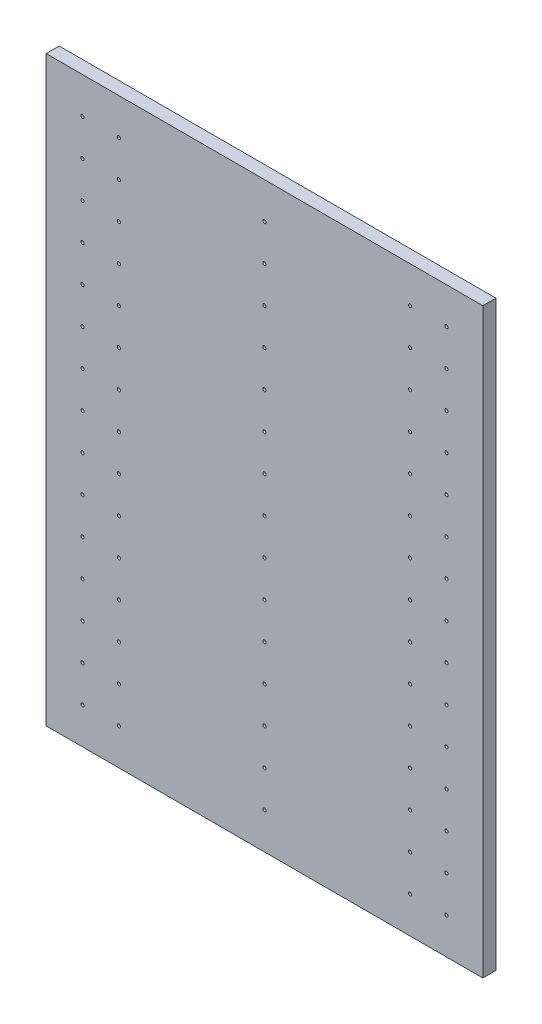
SolidWorks part; units mm, degrees
ref_plane "Спереди" through (0, 0, 0) normal (0, 0, 1) x (1, 0, 0)
ref_plane "Сверху" through (0, 0, 0) normal (0, 1, 0) x (1, 0, 0)
ref_plane "Справа" through (0, 0, 0) normal (1, 0, 0) x (0, 0, -1)
sketch "Эскиз1" plane through (0, 0, 0) normal (0, 0, 1) x (1, 0, 0)
  line L1 (0, 0) -> (600, 0)
  line L2 (0, 0) -> (0, 800)
  line L3 (0, 800) -> (600, 800)
  line L4 (600, 0) -> (600, 800)
extrude "Бобышка-Вытянуть1" add sketch "Эскиз1" along normal blind 18
sketch "Эскиз2" plane through (0, 0, 18) normal (0, 0, 1) x (1, 0, 0)
  circle A0 centre (550, 50) radius 2.25
  circle A1 centre (500, 50) radius 2.25
  circle A2 centre (300, 50) radius 2.25
  circle A3 centre (100, 50) radius 2.25
  circle A4 centre (50, 50) radius 2.25
  circle A60 centre (550, 100) radius 2.25
  circle A61 centre (500, 100) radius 2.25
  circle A62 centre (300, 100) radius 2.25
  circle A63 centre (100, 100) radius 2.25
  circle A64 centre (50, 100) radius 2.25
  circle A65 centre (550, 150) radius 2.25
  circle A66 centre (500, 150) radius 2.25
  circle A67 centre (300, 150) radius 2.25
  circle A68 centre (100, 150) radius 2.25
  circle A69 centre (50, 150) radius 2.25
  circle A70 centre (550, 200) radius 2.25
  circle A71 centre (500, 200) radius 2.25
  circle A72 centre (300, 200) radius 2.25
  circle A73 centre (100, 200) radius 2.25
  circle A74 centre (50, 200) radius 2.25
  circle A75 centre (550, 250) radius 2.25
  circle A76 centre (500, 250) radius 2.25
  circle A77 centre (300, 250) radius 2.25
  circle A78 centre (100, 250) radius 2.25
  circle A79 centre (50, 250) radius 2.25
  circle A80 centre (550, 300) radius 2.25
  circle A81 centre (500, 300) radius 2.25
  circle A82 centre (300, 300) radius 2.25
  circle A83 centre (100, 300) radius 2.25
  circle A84 centre (50, 300) radius 2.25
  circle A85 centre (550, 350) radius 2.25
  circle A86 centre (500, 350) radius 2.25
  circle A87 centre (300, 350) radius 2.25
  circle A88 centre (100, 350) radius 2.25
  circle A89 centre (50, 350) radius 2.25
  circle A90 centre (550, 400) radius 2.25
  circle A91 centre (500, 400) radius 2.25
  circle A92 centre (300, 400) radius 2.25
  circle A93 centre (100, 400) radius 2.25
  circle A94 centre (50, 400) radius 2.25
  circle A95 centre (550, 450) radius 2.25
  circle A96 centre (500, 450) radius 2.25
  circle A97 centre (300, 450) radius 2.25
  circle A98 centre (100, 450) radius 2.25
  circle A99 centre (50, 450) radius 2.25
  circle A100 centre (550, 500) radius 2.25
  circle A101 centre (500, 500) radius 2.25
  circle A102 centre (300, 500) radius 2.25
  circle A103 centre (100, 500) radius 2.25
  circle A104 centre (50, 500) radius 2.25
  circle A105 centre (550, 550) radius 2.25
  circle A106 centre (500, 550) radius 2.25
  circle A107 centre (300, 550) radius 2.25
  circle A108 centre (100, 550) radius 2.25
  circle A109 centre (50, 550) radius 2.25
  circle A110 centre (550, 600) radius 2.25
  circle A111 centre (500, 600) radius 2.25
  circle A112 centre (300, 600) radius 2.25
  circle A113 centre (100, 600) radius 2.25
  circle A114 centre (50, 600) radius 2.25
  circle A115 centre (550, 650) radius 2.25
  circle A116 centre (500, 650) radius 2.25
  circle A117 centre (300, 650) radius 2.25
  circle A118 centre (100, 650) radius 2.25
  circle A119 centre (50, 650) radius 2.25
  circle A120 centre (550, 700) radius 2.25
  circle A121 centre (500, 700) radius 2.25
  circle A122 centre (300, 700) radius 2.25
  circle A123 centre (100, 700) radius 2.25
  circle A124 centre (50, 700) radius 2.25
  circle A125 centre (550, 750) radius 2.25
  circle A126 centre (500, 750) radius 2.25
  circle A127 centre (300, 750) radius 2.25
  circle A128 centre (100, 750) radius 2.25
  circle A129 centre (50, 750) radius 2.25
  dimension "D1" = 15
extrude "Вырез-Вытянуть1" cut sketch "Эскиз2" against normal blind 9
